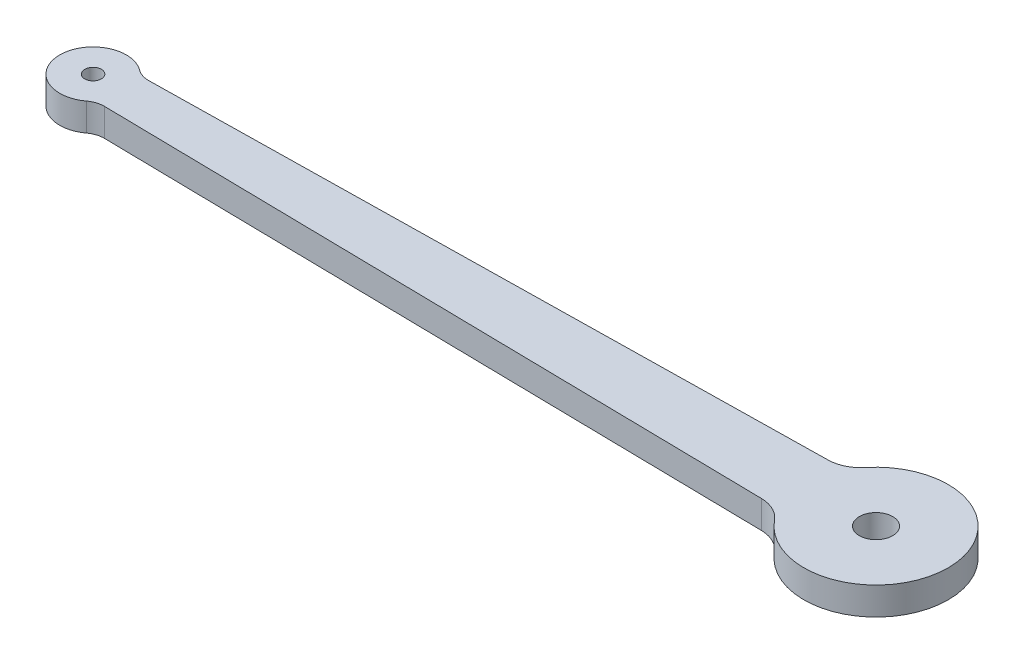
SolidWorks part; units mm, degrees
material "6061 Alloy"
ref_plane "Front Plane" through (0, 0, 0) normal (0, 0, 1) x (1, 0, 0)
ref_plane "Top Plane" through (0, 0, 0) normal (0, 1, 0) x (1, 0, 0)
ref_plane "Right Plane" through (0, 0, 0) normal (1, 0, 0) x (0, 0, -1)
sketch "Sketch1" plane through (0, 0, 0) normal (0, 1, 0) x (1, 0, 0)
  line L0 (-35.25, 0) -> (35.25, 0) construction
  line L1 (-32.2164, 2) -> (27.9341, 3)
  line L2 (-32.2164, -2) -> (27.9341, -3)
  line L3 (27.9341, 3) -> (27.9341, -3) construction
  line L4 (0, 0) -> (27.9341, 0) construction
  line L5 (-32.2164, 2) -> (-32.2164, -2) construction
  line L6 (0, 0) -> (-32.2164, 0) construction
  arc A0 (-33.4498, 2.3998) -> (-33.4498, -2.3998) centre (-35.25, 0) ccw
  arc A1 (30.2102, -4.105) -> (30.2102, 4.105) centre (35.25, 0) ccw
  arc A2 (27.9341, -3) -> (30.2102, -4.105) centre (27.8842, -5.9996) cw
  arc A3 (27.9341, 3) -> (30.2102, 4.105) centre (27.8842, 5.9996) ccw
  arc A4 (-32.2164, -2) -> (-33.4498, -2.3998) centre (-32.2496, -3.9997) ccw
  arc A5 (-32.2164, 2) -> (-33.4498, 2.3998) centre (-32.2496, 3.9997) cw
  dimension "D1" = 13
  dimension "D2" = 6
  dimension "D6" = 3
  dimension "D7" = 2
  dimension "D3" = 70.5
  dimension "D4" = 6
  dimension "D5" = 4
extrude "Boss-Extrude1" add sketch "Sketch1" along normal blind 2.5
sketch "Sketch2" plane through (0, 2.5, 0) normal (0, 1, 0) x (1, 0, 0)
  circle A0 centre (-35.25, 0) radius 0.75
  circle A1 centre (35.25, 0) radius 1.5
  dimension "D1" = 3
  dimension "D2" = 1.5
extrude "Cut-Extrude1" cut sketch "Sketch2" against normal up to next contours A0 | A1
ref_plane "Mid Plane Mate Plane" through (0, 1.25, 0) normal (0, 1, 0) x (-1, 0, 0)
